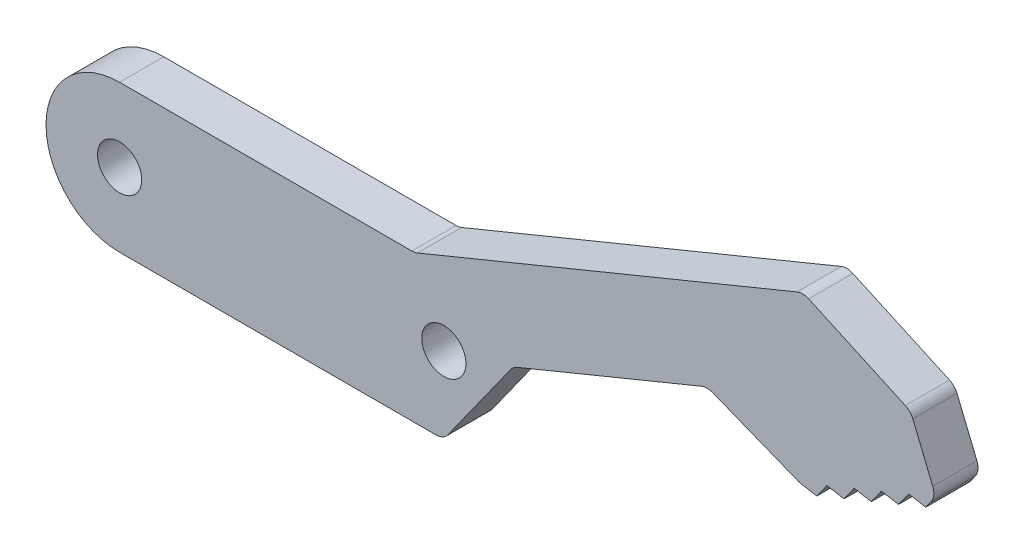
SolidWorks part; units mm, degrees
ref_plane "Front Plane" through (0, 0, 0) normal (0, 0, 1) x (1, 0, 0)
ref_plane "Top Plane" through (0, 0, 0) normal (0, 1, 0) x (1, 0, 0)
ref_plane "Right Plane" through (0, 0, 0) normal (1, 0, 0) x (0, 0, -1)
sketch "Sketch1" plane through (0, 0, 0) normal (0, 0, 1) x (1, 0, 0)
  line L0 (0, 0) -> (22, 0) construction
  line L1 (0, 5) -> (22, 5)
  line L2 (0, -5) -> (22, -5)
  line L3 (20.05, 5) -> (23.9914, -4.5863) construction
  line L4 (20.05, 5) -> (51.4959, 17.929) construction
  line L5 (23.9914, -4.5863) -> (55.4373, 8.3426) construction
  line L6 (51.4959, 17.929) -> (55.4373, 8.3426) construction
  line L7 (20.05, 5) -> (46.409, 15.8375)
  line L8 (46.409, 15.8375) -> (53.7261, 12.5046)
  line L9 (53.7261, 12.5046) -> (55.4373, 8.3426)
  line L10 (46.1885, 4.54) -> (39.9002, 7.0361)
  line L11 (39.9002, 7.0361) -> (26.7299, 1.6211)
  line L12 (46.1885, 4.54) -> (55.4373, 8.3426) construction
  line L13 (46.1885, 4.54) -> (47.3529, 4.3376)
  line L14 (47.3529, 4.3376) -> (48.0382, 5.3005)
  line L15 (47.3529, 4.3376) -> (54.752, 7.3797) construction
  line L16 (48.0382, 5.3005) -> (49.2027, 5.0981)
  line L17 (49.2027, 5.0981) -> (49.888, 6.0611)
  line L18 (49.888, 6.0611) -> (51.0524, 5.8587)
  line L19 (51.0524, 5.8587) -> (51.7378, 6.8216)
  line L20 (51.7378, 6.8216) -> (52.9022, 6.6192)
  line L21 (52.9022, 6.6192) -> (53.5875, 7.5821)
  line L22 (53.5875, 7.5821) -> (54.752, 7.3797)
  line L23 (54.752, 7.3797) -> (55.4373, 8.3426)
  line L24 (26.7299, 1.6211) -> (22, -5)
  arc A0 (0, 5) -> (0, -5) centre (0, 0) ccw
  arc A1 (22, -5) -> (22, 5) centre (22, 0) ccw
  circle A2 centre (0, 0) radius 1.5
  circle A3 centre (22.0207, 0.2068) radius 1.5
  point P3 (11, 0)
  dimension "D11" = 3
  dimension "D1" = 10
  dimension "D2" = 22
  dimension "D3" = 157.65
  dimension "D4" = 1.95
  dimension "D5" = 34
  dimension "D6" = 5.5
  dimension "D7" = 4.5
  dimension "D8" = 10
  dimension "D9" = 136
  dimension "D10" = 14.24
  dimension "D12" = 2
  dimension "D13" = 0.63
  dimension "D14" = 8
extrude "Boss-Extrude3" add sketch "Sketch1" along normal blind 3 contours A1 L1 A0 L2 A3 A2 | A1 L11 L10 L13 L14 L16 L17 L18 L19 L20 L21 L22 L23 L9 L8 L7 L1
fillet "Fillet1" radius 1 8 edges at (46.1885, 4.54, 1.5) (39.9002, 7.0361, 1.5) (53.7261, 12.5046, 1.5) (55.4373, 8.3426, 1.5) (46.409, 15.8375, 1.5) (20.05, 5, 1.5) (26.7299, 1.6211, 1.5) (22, -5, 1.5)
